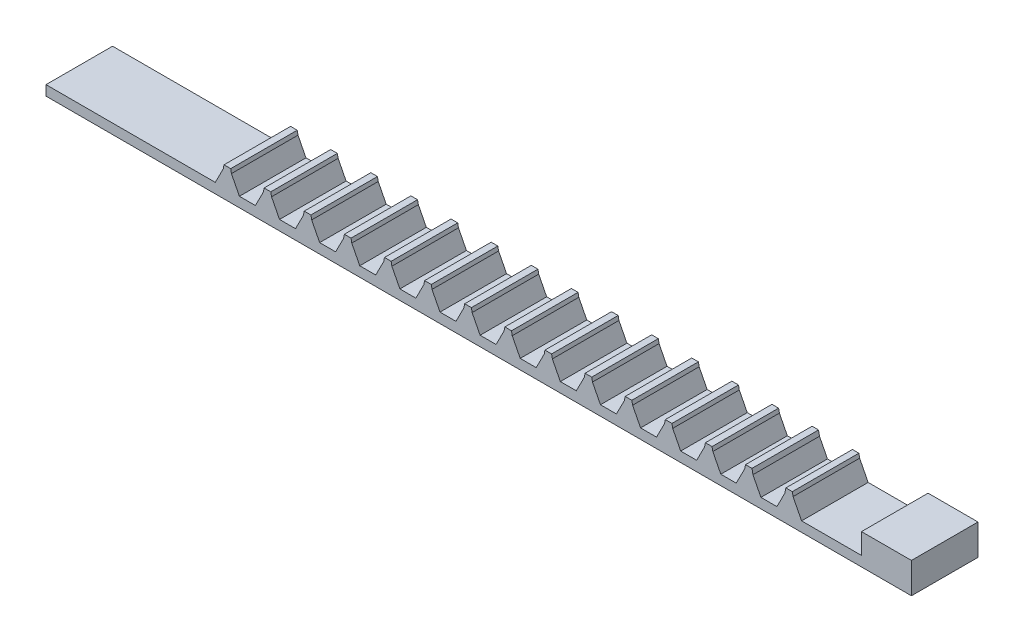
SolidWorks part; units mm, degrees
material "Gray Cast Iron"
ref_plane "Front Plane" through (0, 0, 0) normal (0, 0, 1) x (1, 0, 0)
ref_plane "Top Plane" through (0, 0, 0) normal (0, 1, 0) x (1, 0, 0)
ref_plane "Right Plane" through (0, 0, 0) normal (1, 0, 0) x (0, 0, -1)
sketch "Sketch1" plane through (0, 0, 0) normal (0, 1, 0) x (1, 0, 0)
  line L1 (-120.3493, 37.937) -> (-54.3093, 37.937)
  line L3 (-120.3493, 32.857) -> (-54.3093, 32.857)
  line L4 (-54.3093, 37.937) -> (-54.3093, 32.857)
  line L5 (-120.3493, 37.937) -> (-120.3493, 32.857)
extrude "Boss-Extrude1" add sketch "Sketch1" along normal blind 3.81
sketch "Sketch2" plane through (0, 0, -32.857) normal (0, 0, 1) x (1, 0, 0)
  line L0 (-62.6913, 3.81) -> (-58.1193, 3.81)
  line L1 (-120.3493, 3.81) -> (-54.3093, 3.81) construction
  line L3 (-120.3493, 0) -> (-54.3093, 0) construction
  line L4 (-58.1193, 0) -> (-62.6913, 0)
  line L7 (-58.1193, 0.762) -> (-62.6913, 0.762)
  line L8 (-62.6913, 0.762) -> (-62.6913, 3.81)
  line L9 (-58.1193, 3.81) -> (-58.1193, 0.762)
extrude "Cut-Extrude1" cut sketch "Sketch2" against normal through all contours L9 L7 L8 L0
chamfer "Chamfer1" distance 0.254 angle 45 2 edges at (-54.3093, 3.81, -35.397) (-58.1193, 3.81, -35.397)
sketch "Sketch4" plane through (0, 0, -32.857) normal (0, 0, 1) x (1, 0, 0)
  line L94 (-64.5754, 0.762) -> (-65.7946, 0.762)
  line L122 (-67.6788, 0.762) -> (-68.8559, 0.762)
  line L130 (-70.6979, 0.762) -> (-71.9171, 0.762)
  line L143 (-120.3493, 3.81) -> (-62.6913, 3.81) construction
  line L147 (-73.7591, 0.762) -> (-74.9783, 0.762)
  line L148 (-76.8203, 0.762) -> (-78.0395, 0.762)
  line L152 (-79.8816, 0.762) -> (-81.1008, 0.762)
  line L153 (-89.0653, 0.762) -> (-90.2845, 0.762)
  line L159 (-86.004, 0.762) -> (-87.2232, 0.762)
  line L164 (-82.9428, 0.762) -> (-84.162, 0.762)
  line L165 (-106.2576, 3.81) -> (-62.6913, 3.81)
  line L194 (-101.3102, 0.762) -> (-102.5294, 0.762)
  line L200 (-98.2489, 0.762) -> (-99.4681, 0.762)
  line L201 (-104.3714, 0.762) -> (-105.5906, 0.762)
  line L204 (-92.1265, 0.762) -> (-93.3457, 0.762)
  line L207 (-104.981, 0.762) -> (-104.981, 1.2897)
  line L208 (-106.7656, 2.2561) -> (-106.2576, 2.2561)
  line L210 (-95.1877, 0.762) -> (-96.4069, 0.762)
  line L213 (-106.8238, 1.9569) -> (-107.4326, 0.762)
  line L215 (-106.7656, 2.2561) -> (-106.8238, 1.9569)
  line L216 (-107.4326, 0.762) -> (-107.4326, 3.81)
  line L225 (-107.4326, 3.81) -> (-106.2576, 3.81)
  line L227 (-62.6913, 0.762) -> (-62.6913, 3.81)
  line L228 (-90.9515, 2.2561) -> (-91.4595, 2.2561)
  line L229 (-103.7044, 2.2561) -> (-103.7625, 1.9569)
  line L230 (-97.6401, 1.9569) -> (-98.2489, 0.762)
  line L231 (-103.1964, 2.2561) -> (-103.1382, 1.9569)
  line L232 (-103.7625, 1.9569) -> (-104.3714, 0.762)
  line L233 (-100.7013, 1.9569) -> (-101.3102, 0.762)
  line L234 (-100.1352, 2.2561) -> (-100.077, 1.9569)
  line L235 (-103.1382, 1.9569) -> (-102.5294, 0.762)
  line L236 (-100.1352, 2.2561) -> (-100.6432, 2.2561)
  line L237 (-106.1995, 1.9569) -> (-105.5906, 0.762)
  line L238 (-100.077, 1.9569) -> (-99.4681, 0.762)
  line L239 (-94.5789, 1.9569) -> (-95.1877, 0.762)
  line L240 (-94.0127, 2.2561) -> (-93.9545, 1.9569)
  line L241 (-94.0127, 2.2561) -> (-94.5207, 2.2561)
  line L242 (-91.5176, 1.9569) -> (-92.1265, 0.762)
  line L243 (-97.5819, 2.2561) -> (-97.6401, 1.9569)
  line L244 (-94.5207, 2.2561) -> (-94.5789, 1.9569)
  line L245 (-100.6432, 2.2561) -> (-100.7013, 1.9569)
  line L246 (-97.0158, 1.9569) -> (-96.4069, 0.762)
  line L247 (-97.0739, 2.2561) -> (-97.5819, 2.2561)
  line L248 (-91.4595, 2.2561) -> (-91.5176, 1.9569)
  line L249 (-103.1964, 2.2561) -> (-103.7044, 2.2561)
  line L250 (-93.9545, 1.9569) -> (-93.3457, 0.762)
  line L251 (-106.2576, 2.2561) -> (-106.1995, 1.9569)
  line L252 (-97.0739, 2.2561) -> (-97.0158, 1.9569)
  line L253 (-88.3982, 2.2561) -> (-88.4564, 1.9569)
  line L254 (-87.8902, 2.2561) -> (-87.8321, 1.9569)
  line L255 (-84.7709, 1.9569) -> (-84.162, 0.762)
  line L256 (-82.3339, 1.9569) -> (-82.9428, 0.762)
  line L257 (-84.829, 2.2561) -> (-84.7709, 1.9569)
  line L258 (-78.7066, 2.2561) -> (-79.2146, 2.2561)
  line L259 (-81.7678, 2.2561) -> (-82.2758, 2.2561)
  line L260 (-85.337, 2.2561) -> (-85.3952, 1.9569)
  line L261 (-79.2727, 1.9569) -> (-79.8816, 0.762)
  line L262 (-81.7096, 1.9569) -> (-81.1008, 0.762)
  line L263 (-87.8321, 1.9569) -> (-87.2232, 0.762)
  line L264 (-87.8902, 2.2561) -> (-88.3982, 2.2561)
  line L265 (-81.7678, 2.2561) -> (-81.7096, 1.9569)
  line L266 (-85.3952, 1.9569) -> (-86.004, 0.762)
  line L267 (-84.829, 2.2561) -> (-85.337, 2.2561)
  line L268 (-82.2758, 2.2561) -> (-82.3339, 1.9569)
  line L269 (-88.4564, 1.9569) -> (-89.0653, 0.762)
  line L270 (-79.2146, 2.2561) -> (-79.2727, 1.9569)
  line L271 (-90.8933, 1.9569) -> (-90.2845, 0.762)
  line L272 (-90.9515, 2.2561) -> (-90.8933, 1.9569)
  line L273 (-75.5872, 1.9569) -> (-74.9783, 0.762)
  line L274 (-78.6484, 1.9569) -> (-78.0395, 0.762)
  line L275 (-73.1503, 1.9569) -> (-73.7591, 0.762)
  line L276 (-76.2115, 1.9569) -> (-76.8203, 0.762)
  line L277 (-73.0921, 2.2561) -> (-73.1503, 1.9569)
  line L278 (-76.1533, 2.2561) -> (-76.2115, 1.9569)
  line L279 (-75.6453, 2.2561) -> (-76.1533, 2.2561)
  line L280 (-78.7066, 2.2561) -> (-78.6484, 1.9569)
  line L281 (-72.5841, 2.2561) -> (-73.0921, 2.2561)
  line L282 (-75.6453, 2.2561) -> (-75.5872, 1.9569)
  line L283 (-70.0309, 2.2561) -> (-70.089, 1.9569)
  line L284 (-69.5229, 2.2561) -> (-70.0309, 2.2561)
  line L285 (-72.5259, 1.9569) -> (-71.9171, 0.762)
  line L286 (-70.089, 1.9569) -> (-70.6979, 0.762)
  line L287 (-72.5841, 2.2561) -> (-72.5259, 1.9569)
  line L288 (-69.5229, 2.2561) -> (-69.4647, 1.9569)
  line L289 (-67.0278, 2.0397) -> (-67.6788, 0.762)
  line L290 (-66.9696, 2.3389) -> (-67.0278, 2.0397)
  line L291 (-69.4647, 1.9569) -> (-68.8559, 0.762)
  line L292 (-66.4035, 1.9569) -> (-65.7946, 0.762)
  line L293 (-66.4777, 2.3389) -> (-66.4035, 1.9569)
  line L294 (-66.4777, 2.3389) -> (-66.9696, 2.3389)
  line L295 (-63.9666, 1.9569) -> (-64.5754, 0.762)
  line L297 (-63.8923, 2.3389) -> (-63.4004, 2.3389)
  line L298 (-63.4004, 2.3389) -> (-63.3422, 2.0397)
  line L299 (-63.3422, 2.0397) -> (-62.6913, 0.762)
  line L300 (-63.8923, 2.3389) -> (-63.9666, 1.9569)
  point P57 (-104.981, 0.762)
  point P67 (-98.8585, 0.762)
  point P87 (-101.9198, 0.762)
  point P99 (-95.7973, 0.762)
  point P107 (-92.7361, 0.762)
  point P155 (-89.6749, 0.762)
  point P156 (-83.5524, 0.762)
  point P157 (-86.6136, 0.762)
  point P158 (-80.4912, 0.762)
  point P164 (-74.3687, 0.762)
  point P168 (-77.4299, 0.762)
  point P174 (-71.3075, 0.762)
  point P178 (-68.2673, 0.762)
  point P181 (-65.185, 0.762)
extrude "Cut-Extrude2" cut sketch "Sketch4" against normal through all contours L253 L269 L153 L271 L272 L228 L248 L242 L204 L250 L240 L241 L244 L239 L210 L246 L252 L247 L243 L230 L200 L238 L234 L236 L245 L233 L194 L235 L231 L249 L229 L232 L201 L237 L251 L208 L215 L213 L216 L225 L165 L227 L299 L298 L297 L300 L295 L94 L292 L293 L294 L290 L289 L122 L291 L288 L284 L283 L286 L130 L285 L287 L281 L277 L275 L147 L273 L282 L279 L278 L276 L148 L274 L280 L258 L270 L261 L152 L262 L265 L259 L268 L256 L164 L255 L257 L267 L260 L266 L159 L263 L254 L264
sketch "Sketch5" plane through (0, 0, -32.857) normal (0, 0, 1) x (1, 0, 0)
  line L1 (-107.4326, 0.762) -> (-120.3493, 0.762)
  line L6 (-120.3493, 3.81) -> (-120.3493, 0) construction
  line L7 (-120.3493, 0.762) -> (-120.3493, 3.81)
  line L10 (-107.4326, 0.762) -> (-107.4326, 3.81)
  line L11 (-107.4326, 3.81) -> (-120.3493, 3.81)
extrude "Cut-Extrude3" cut sketch "Sketch5" against normal through all
sketch "Sketch6" plane through (0, 0, -32.857) normal (0, 0, 1) x (1, 0, 0)
  line L0 (-58.1193, 2.3389) -> (-54.3093, 2.3389)
  line L2 (-58.1193, 2.3389) -> (-58.1193, 4.0656)
  line L3 (-58.1193, 3.556) -> (-58.1193, 0.762) construction
  line L4 (-54.3093, 2.3389) -> (-54.3093, 4.0656)
  line L5 (-54.3093, 3.556) -> (-54.3093, 0) construction
  line L6 (-54.3093, 4.0656) -> (-58.1193, 4.0656)
extrude "Cut-Extrude4" cut sketch "Sketch6" against normal through all
